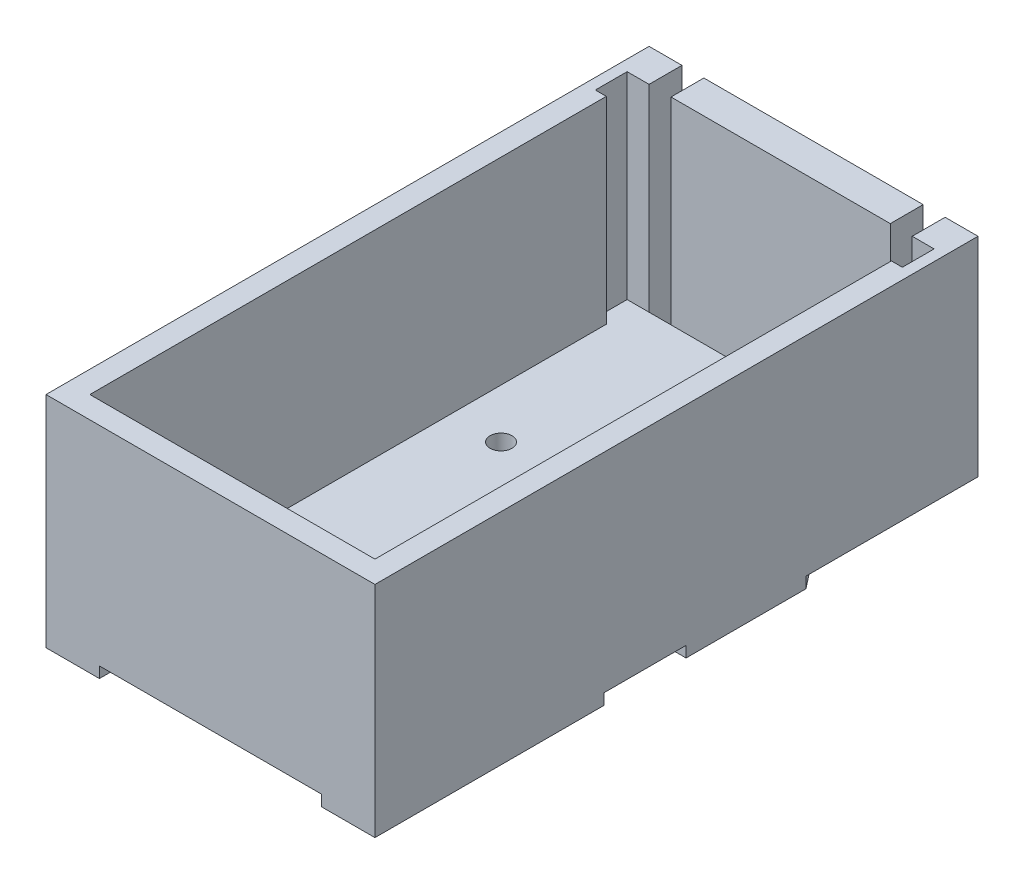
SolidWorks part; units mm, degrees
material "CA"
ref_plane "Front Plane" through (0, 0, 0) normal (0, 0, 1) x (1, 0, 0)
ref_plane "Top Plane" through (0, 0, 0) normal (0, 1, 0) x (1, 0, 0)
ref_plane "Right Plane" through (0, 0, 0) normal (1, 0, 0) x (0, 0, -1)
sketch "Sketch1" plane through (0, 0, 0) normal (0, 1, 0) x (1, 0, 0)
  line L1 (0, 0) -> (30, 0)
  line L2 (0, 0) -> (0, 55)
  line L3 (0, 55) -> (30, 55)
  line L4 (30, 0) -> (30, 55)
  dimension "D1" = 30
  dimension "D2" = 55
extrude "Boss-Extrude1" add sketch "Sketch1" along normal blind 20
sketch "Sketch2" plane through (0, 20, 0) normal (0, 1, 0) x (-1, 0, 0)
  line L0 (-15, -55) -> (-15, 0) construction
  line L1 (-30, -55) -> (0, -55) construction
  line L2 (0, 0) -> (-30, 0) construction
  line L3 (-29, -52) -> (-1, -52)
  line L4 (-1, -52) -> (-1, -49.1016)
  line L5 (-1, -49.1016) -> (-2, -49.1016)
  line L6 (-2, -49.1016) -> (-2, -2)
  line L7 (-2, -2) -> (-28, -2)
  line L8 (0, -55) -> (0, 0) construction
  line L9 (-28, -49.1016) -> (-28, -2)
  line L10 (-29, -49.1016) -> (-28, -49.1016)
  line L11 (-29, -52) -> (-29, -49.1016)
  point P15 (-15, -2)
  point P18 (-15, -52)
  dimension "D1" = 2
  dimension "D2" = 2
  dimension "D3" = 3
  dimension "D4" = 1
extrude "Cut-Extrude1" cut sketch "Sketch2" against normal blind 18
sketch "Sketch3" plane through (0, 20, 0) normal (0, 1, 0) x (-1, 0, 0)
  line L0 (-30, -55) -> (0, -55) construction
  line L1 (-3, -55) -> (-5, -55)
  line L2 (-3, -55) -> (-3, -52)
  line L3 (-3, -52) -> (-5, -52)
  line L4 (-5, -55) -> (-5, -52)
  line L5 (-29, -52) -> (-1, -52) construction
  line L6 (0, -55) -> (0, 0) construction
  line L7 (-15, -55) -> (-15, 0) construction
  line L8 (0, 0) -> (-30, 0) construction
  line L9 (-25, -55) -> (-25, -52)
  line L10 (-27, -52) -> (-25, -52)
  line L11 (-27, -55) -> (-27, -52)
  line L12 (-27, -55) -> (-25, -55)
  dimension "D1" = 2
  dimension "D2" = 3
extrude "Cut-Extrude2" cut sketch "Sketch3" against normal through all
sketch "Sketch4" plane through (0, 0, -55) normal (0, 0, -1) x (-1, 0, 0)
  line L0 (-15, 0) -> (-15, 20) construction
  line L1 (-23, 18) -> (-16, 18)
  line L2 (-23, 18) -> (-23, 2)
  line L3 (-23, 2) -> (-16, 2)
  line L4 (-16, 18) -> (-16, 2)
  line L5 (-25, 0) -> (-5, 0) construction
  line L6 (-25, 20) -> (-5, 20) construction
  line L7 (-25, 0) -> (-25, 20) construction
  line L8 (-14, 18) -> (-14, 2)
  line L9 (-7, 2) -> (-14, 2)
  line L10 (-7, 18) -> (-14, 18)
  line L11 (-7, 18) -> (-7, 2)
  dimension "D1" = 2
  dimension "D2" = 2
  dimension "D3" = 1
  dimension "D4" = 2
extrude "Cut-Extrude3" cut sketch "Sketch4" against normal blind 1
sketch "Sketch5" plane through (0, 0, 0) normal (0, -1, 0) x (1, 0, 0)
  line L0 (15, 0) -> (15, -55) construction
  line L1 (0, 0) -> (30, 0) construction
  line L2 (25, -55) -> (5, -55) construction
  circle A0 centre (6.5, -14) radius 1
  circle A4 centre (23.5, -14) radius 1
  circle A5 centre (6.5, -35) radius 1
  circle A6 centre (23.5, -35) radius 1
  dimension "D1" = 2
  dimension "D3" = 14
  dimension "D2" = 8.5
  dimension "D4" = 2
  dimension "D5" = 2
extrude "Cut-Extrude4" cut sketch "Sketch5" against normal through all
sketch "Sketch6" plane through (0, 0, 0) normal (0, -1, 0) x (1, 0, 0)
  line L0 (15, 0) -> (15, -55) construction
  line L1 (0, 0) -> (30, 0) construction
  line L2 (25, -55) -> (5, -55) construction
  line L3 (4.8718, 0) -> (4.8718, -2.9329)
  line L4 (4.8718, -2.9329) -> (7.8857, -2.9329)
  line L5 (7.8857, -2.9329) -> (7.8857, -12.1149)
  line L6 (7.8857, -12.1149) -> (12.0912, -12.1149)
  line L7 (12.0912, -12.1149) -> (12.0912, -13.8672)
  line L8 (12.0912, -13.8672) -> (17.9088, -13.8672)
  line L9 (4.8718, 0) -> (25.1282, 0)
  line L10 (0, -20.8763) -> (3.6802, -20.8763)
  line L11 (0, -55) -> (0, 0) construction
  line L12 (3.6802, -20.8763) -> (3.6802, -22.6987)
  line L13 (3.6802, -22.6987) -> (6.8343, -22.6987)
  line L14 (6.8343, -22.6987) -> (6.8343, -20.8763)
  line L15 (6.8343, -20.8763) -> (23.1657, -20.8763)
  line L16 (0, -20.8763) -> (0, -28.3761)
  line L17 (0, -28.3761) -> (3.6802, -28.3761)
  line L18 (3.6802, -28.3761) -> (3.6802, -26.2033)
  line L19 (3.6802, -26.2033) -> (6.8343, -26.2033)
  line L20 (6.8343, -26.2033) -> (6.8343, -28.3761)
  line L21 (6.8343, -28.3761) -> (23.1657, -28.3761)
  line L22 (0, -39.3104) -> (3.6802, -44.0066)
  line L23 (3.6802, -44.0066) -> (5.7129, -44.0066)
  line L24 (5.7129, -44.0066) -> (6.8343, -42.8851)
  line L25 (6.8343, -42.8851) -> (6.8343, -39.8011)
  line L26 (6.8343, -39.8011) -> (23.1657, -39.8011)
  line L27 (0, -39.3104) -> (0, -55)
  line L28 (0, -55) -> (1.8401, -55)
  line L29 (3, -55) -> (0, -55) construction
  line L30 (1.8401, -55) -> (1.8401, -51.4363)
  line L31 (1.8401, -51.4363) -> (28.1599, -51.4363)
  line L32 (15, -51.4363) -> (15, -39.8011)
  line L33 (28.1599, -55) -> (28.1599, -51.4363)
  line L34 (30, -55) -> (28.1599, -55)
  line L35 (30, -39.3104) -> (30, -55)
  line L36 (23.1657, -42.8851) -> (23.1657, -39.8011)
  line L37 (24.2871, -44.0066) -> (23.1657, -42.8851)
  line L38 (26.3198, -44.0066) -> (24.2871, -44.0066)
  line L39 (30, -39.3104) -> (26.3198, -44.0066)
  line L40 (23.1657, -26.2033) -> (23.1657, -28.3761)
  line L41 (26.3198, -26.2033) -> (23.1657, -26.2033)
  line L42 (26.3198, -28.3761) -> (26.3198, -26.2033)
  line L43 (30, -28.3761) -> (26.3198, -28.3761)
  line L44 (30, -20.8763) -> (30, -28.3761)
  line L45 (23.1657, -22.6987) -> (23.1657, -20.8763)
  line L46 (26.3198, -22.6987) -> (23.1657, -22.6987)
  line L47 (26.3198, -20.8763) -> (26.3198, -22.6987)
  line L48 (30, -20.8763) -> (26.3198, -20.8763)
  line L49 (17.9088, -12.1149) -> (17.9088, -13.8672)
  line L50 (22.1143, -12.1149) -> (17.9088, -12.1149)
  line L51 (22.1143, -2.9329) -> (22.1143, -12.1149)
  line L52 (25.1282, -2.9329) -> (22.1143, -2.9329)
  line L53 (25.1282, 0) -> (25.1282, -2.9329)
  line L54 (4.8718, 0) -> (25.1282, 0)
  point P49 (15, -28.3761)
  point P55 (15, -20.8763)
  point P60 (15, -13.8672)
  line M6 (27, -55) -> (30, -55)
  line M7 (30, -55) -> (30, 0)
  line M8 (30, 0) -> (0, 0)
  line M9 (0, 0) -> (0, -55)
  line M10 (0, -55) -> (3, -55)
extrude "Cut-Extrude5" cut sketch "Sketch6" against normal blind 1 contours L0 L54 L3 L4 L5 L6 L7 L8 | L0 L8 L49 L50 L51 L52 L53 M8 | L0 L15 L14 L13 L12 L10 L17 L18 L19 L20 L21 M9 | L15 L0 L21 L40 L41 L42 L43 L48 L47 L46 L45 M7 | L31 L32 L26 L25 L24 L23 L22 L30 M9 M10 | L39 L38 L37 L36 L26 L32 L31 L33 M7 M6
